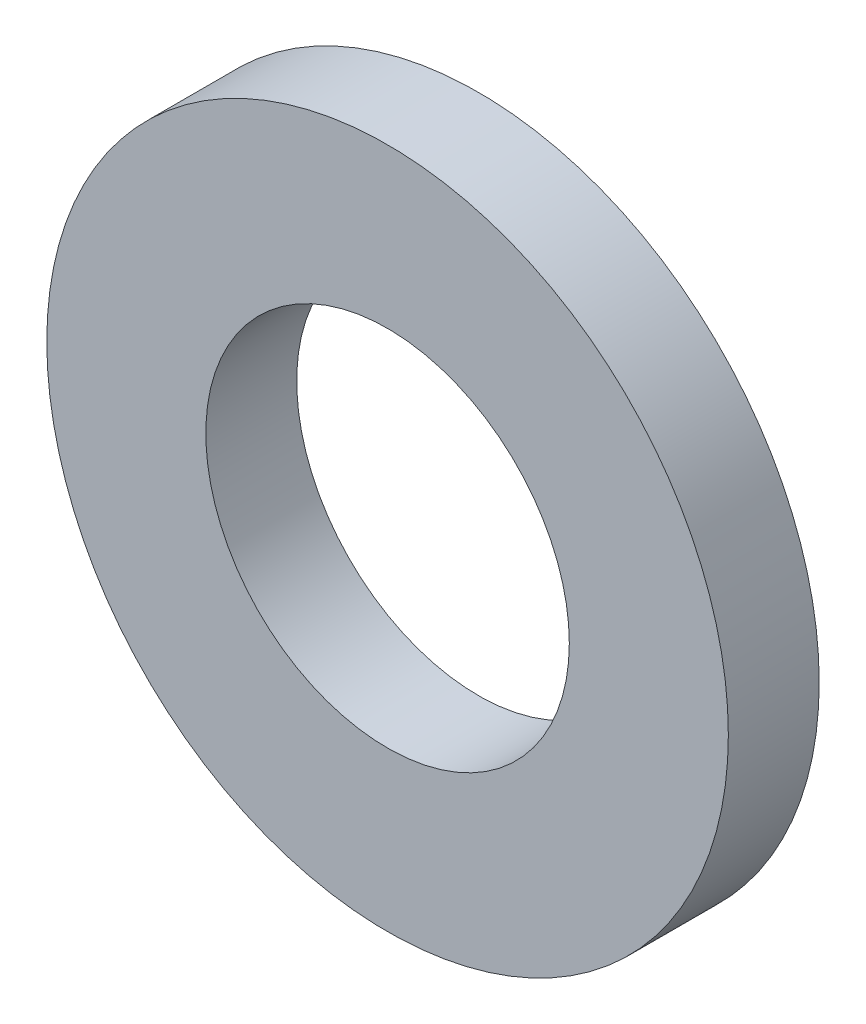
SolidWorks part; units mm, degrees
ref_plane "Front Plane" through (0, 0, 0) normal (0, 0, 1) x (1, 0, 0)
ref_plane "Top Plane" through (0, 0, 0) normal (0, 1, 0) x (1, 0, 0)
ref_plane "Right Plane" through (0, 0, 0) normal (1, 0, 0) x (0, 0, -1)
sketch "Sketch1" plane through (0, 0, 0) normal (0, 0, 1) x (1, 0, 0)
  line L0 (0, 0) -> (0, -3.2) construction
  line L1 (0, 0) -> (2.2627, -2.2627) construction
  circle A0 centre (0, 0) radius 6
  circle A1 centre (0, 0) radius 3.2
  point P5 (6, 0)
  point P6 (3.2, 0)
  point P7 (-3.2, 0)
  point P8 (-6, 0)
  point P9 (0, 6)
  point P10 (0, 3.2)
  point P11 (0, -6)
  point P12 (0, -3.2)
  point P13 (2.2627, -2.2627)
  dimension "D1" = 45
  dimension "OD" = 12
  dimension "ID1" = 6.4
sketch "Sketch2" plane through (0, 0, 0) normal (1, 0, 0) x (0, 0, -1)
  line L0 (-0.8, 6) -> (0.8, 6) construction
  point P2 (0, 6)
  dimension "Thickness" = 1.6
sketch "Sketch3" plane through (0, 0, 0) normal (0, 0, 1) x (1, 0, 0)
  circle A0 centre (0, 0) radius 6 construction
  circle A1 centre (0, 0) radius 3.2 construction
  circle A2 centre (0, 0) radius 6
  circle A3 centre (0, 0) radius 3.2
extrude "Boss-Extrude1" add sketch "Sketch3" along normal up to vertex (0.8 mm away) and the other way up to vertex (0.8 mm away) up to point (0, 6, 0.8) other way up to point (0, 6, -0.8)
